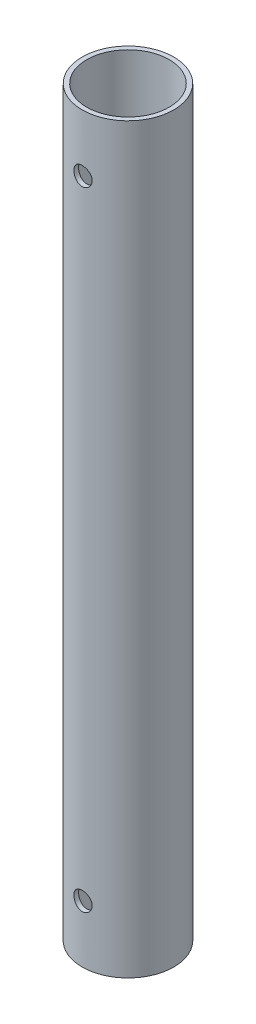
SolidWorks part; units mm, degrees
ref_plane "Front" through (0, 0, 0) normal (0, 0, 1) x (1, 0, 0)
ref_plane "Top" through (0, 0, 0) normal (0, 1, 0) x (1, 0, 0)
ref_plane "Right" through (0, 0, 0) normal (1, 0, 0) x (0, 0, -1)
sketch "Sketch1" plane through (0, 0, 0) normal (0, 1, 0) x (1, 0, 0)
  circle A0 centre (0, 0) radius 10
  circle A1 centre (0, 0) radius 9
  dimension "D1" = 20
  dimension "D2" = 1
extrude "Boss-Extrude1" add sketch "Sketch1" along normal blind 162
ref_plane "Plane1" through (0, 0, 10) normal (0, 0, 1) x (1, 0, 0)
sketch "Sketch3" plane through (0, 0, 10) normal (0, 0, 1) x (1, 0, 0)
  line L0 (0, 162) -> (0, 149.5) construction
  line L1 (10, 162) -> (-10, 162) construction
  line L2 (0, 0) -> (0, 12.5) construction
  circle A0 centre (0, 149.5) radius 2
  circle A1 centre (0, 12.5) radius 2
  dimension "D3" = 4
  dimension "D4" = 4
  dimension "D1" = 12.5
  dimension "D2" = 12.5
extrude "Cut-Extrude2" cut sketch "Sketch3" against normal through all
